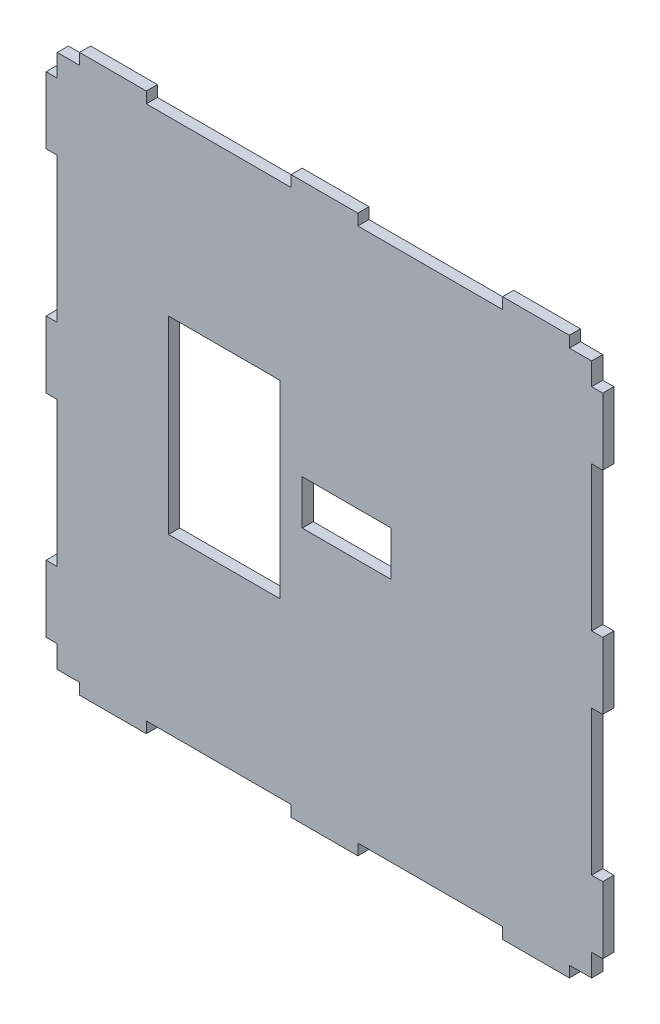
SolidWorks part; units mm, degrees
ref_plane "Front Plane" through (0, 0, 0) normal (0, 0, 1) x (1, 0, 0)
ref_plane "Top Plane" through (0, 0, 0) normal (0, 1, 0) x (1, 0, 0)
ref_plane "Right Plane" through (0, 0, 0) normal (1, 0, 0) x (0, 0, -1)
sketch "Sketch4" plane through (0, 0, 0) normal (0, 0, 1) x (1, 0, 0)
  line L1 (-120, 120) -> (120, 120)
  line L2 (-120, 120) -> (-120, -120)
  line L3 (-120, -120) -> (120, -120)
  line L4 (120, 120) -> (120, -120)
  line L5 (-120, 120) -> (120, -120) construction
  line L6 (-120, -120) -> (120, 120) construction
  line L7 (-110, 120) -> (-80, 120)
  line L8 (-110, 120) -> (-110, 125)
  line L9 (-110, 125) -> (-80, 125)
  line L10 (-80, 120) -> (-80, 125)
  line L11 (-15, 120) -> (15, 120)
  line L12 (-15, 120) -> (-15, 125)
  line L13 (-15, 125) -> (15, 125)
  line L14 (15, 120) -> (15, 125)
  line L15 (80, 120) -> (110, 120)
  line L16 (80, 120) -> (80, 125)
  line L17 (80, 125) -> (110, 125)
  line L18 (110, 120) -> (110, 125)
  line L19 (120, 110) -> (125, 110)
  line L20 (120, 110) -> (120, 80)
  line L21 (120, 80) -> (125, 80)
  line L22 (125, 110) -> (125, 80)
  line L23 (120, 15) -> (125, 15)
  line L24 (120, 15) -> (120, -15)
  line L25 (120, -15) -> (125, -15)
  line L26 (125, 15) -> (125, -15)
  line L27 (120, -80) -> (125, -80)
  line L28 (120, -80) -> (120, -110)
  line L29 (120, -110) -> (125, -110)
  line L30 (125, -80) -> (125, -110)
  line L31 (110, -120) -> (80, -120)
  line L32 (110, -120) -> (110, -125)
  line L33 (110, -125) -> (80, -125)
  line L34 (80, -120) -> (80, -125)
  line L35 (15, -120) -> (-15, -120)
  line L36 (15, -120) -> (15, -125)
  line L37 (15, -125) -> (-15, -125)
  line L38 (-15, -120) -> (-15, -125)
  line L39 (-80, -120) -> (-110, -120)
  line L40 (-80, -120) -> (-80, -125)
  line L41 (-80, -125) -> (-110, -125)
  line L42 (-110, -120) -> (-110, -125)
  line L43 (-120, -110) -> (-125, -110)
  line L44 (-120, -110) -> (-120, -80)
  line L45 (-120, -80) -> (-125, -80)
  line L46 (-125, -110) -> (-125, -80)
  line L47 (-120, -15) -> (-125, -15)
  line L48 (-120, -15) -> (-120, 15)
  line L49 (-120, 15) -> (-125, 15)
  line L50 (-125, -15) -> (-125, 15)
  line L51 (-120, 80) -> (-125, 80)
  line L52 (-120, 80) -> (-120, 110)
  line L53 (-120, 110) -> (-125, 110)
  line L54 (-125, 80) -> (-125, 110)
  point P0 (0, 0)
  dimension "D1" = 240
  dimension "D2" = 240
  dimension "D4" = 30
  dimension "D5" = 5
  dimension "D6" = 10
  dimension "D7" = 65
  dimension "D8" = 30
  dimension "D9" = 5
  dimension "D10" = 65
  dimension "D11" = 30
  dimension "D12" = 5
  dimension "D13" = 5
  dimension "D14" = 30
  dimension "D15" = 30
  dimension "D16" = 30
  dimension "D17" = 5
  dimension "D18" = 5
  dimension "D19" = 65
  dimension "D20" = 10
  dimension "D21" = 65
  dimension "D22" = 30
  dimension "D23" = 5
  dimension "D24" = 5
  dimension "D25" = 5
  dimension "D26" = 30
  dimension "D27" = 30
  dimension "D28" = 10
  dimension "D29" = 65
  dimension "D30" = 65
  dimension "D31" = 30
  dimension "D32" = 30
  dimension "D33" = 30
  dimension "D34" = 5
  dimension "D35" = 5
  dimension "D36" = 5
  dimension "D37" = 10
  dimension "D38" = 65
  dimension "D39" = 65
sketch "Sketch5" plane through (0, 0, 0) normal (0, 0, 1) x (1, 0, 0)
  line L0 (0, 0) -> (44.9824, 0) construction
  line L1 (30, 10) -> (-10, 10)
  line L2 (30, 10) -> (30, -10)
  line L3 (30, -10) -> (-10, -10)
  line L4 (-10, 10) -> (-10, -10)
  line L5 (30, 10) -> (-10, -10) construction
  line L6 (30, -10) -> (-10, 10) construction
  line L7 (0, 0) -> (-83.3437, 0) construction
  line L8 (-120, 120) -> (120, 120)
  line L9 (-70, -42.4723) -> (-20, -42.4723)
  line L10 (-70, -42.4723) -> (-70, 42.4723)
  line L11 (-70, 42.4723) -> (-20, 42.4723)
  line L12 (-20, -42.4723) -> (-20, 42.4723)
  line L13 (-70, -42.4723) -> (-20, 42.4723) construction
  line L14 (-70, 42.4723) -> (-20, -42.4723) construction
  line L15 (120, 120) -> (120, -120)
  line L16 (120, -120) -> (-120, -120)
  line L17 (-120, -120) -> (-120, 120)
  line L18 (-110, 120) -> (-110, 125)
  line L19 (-110, 125) -> (-80, 125)
  line L20 (-80, 125) -> (-80, 120)
  line L21 (-15, 120) -> (-15, 125)
  line L22 (-15, 125) -> (15, 125)
  line L23 (15, 125) -> (15, 120)
  line L24 (80, 120) -> (80, 125)
  line L25 (80, 125) -> (110, 125)
  line L26 (110, 125) -> (110, 120)
  line L27 (120, 110) -> (125, 110)
  line L28 (125, 110) -> (125, 80)
  line L29 (125, 80) -> (120, 80)
  line L30 (120, 15) -> (125, 15)
  line L31 (125, 15) -> (125, -15)
  line L32 (125, -15) -> (120, -15)
  line L33 (120, -80) -> (125, -80)
  line L34 (125, -80) -> (125, -110)
  line L35 (125, -110) -> (120, -110)
  line L36 (110, -120) -> (110, -125)
  line L37 (110, -125) -> (80, -125)
  line L38 (80, -125) -> (80, -120)
  line L39 (15, -120) -> (15, -125)
  line L40 (15, -125) -> (-15, -125)
  line L41 (-15, -125) -> (-15, -120)
  line L42 (-80, -120) -> (-80, -125)
  line L43 (-80, -125) -> (-110, -125)
  line L44 (-110, -125) -> (-110, -120)
  line L45 (-120, -110) -> (-125, -110)
  line L46 (-125, -110) -> (-125, -80)
  line L47 (-125, -80) -> (-120, -80)
  line L48 (-120, -15) -> (-125, -15)
  line L49 (-125, -15) -> (-125, 15)
  line L50 (-125, 15) -> (-120, 15)
  line L51 (-120, 80) -> (-125, 80)
  line L52 (-125, 80) -> (-125, 110)
  line L53 (-125, 110) -> (-120, 110)
  point P0 (10, 0)
  point P8 (22.4912, 0)
  point P10 (-45, 0)
  dimension "D1" = 40
  dimension "D2" = 20
  dimension "D3" = 0
  dimension "D4" = 10
  dimension "D5" = 50
  dimension "D6" = 20
  dimension "D7" = 50
  dimension "D8" = 84.9447
extrude "Boss-Extrude1" add sketch "Sketch5" along normal blind 5 contours L17 L16 L15 L8 L12 L9 L10 L11 L4 L1 L2 L3 | L23 L22 L21 L8 | L26 L25 L24 L8 | L20 L19 L18 L8 | L29 L28 L27 L15 | L32 L31 L30 L15 | L35 L34 L33 L15 | L38 L37 L36 L16 | L41 L40 L39 L16 | L44 L43 L42 L16 | L47 L46 L45 L17 | L50 L49 L48 L17 | L53 L52 L51 L17
